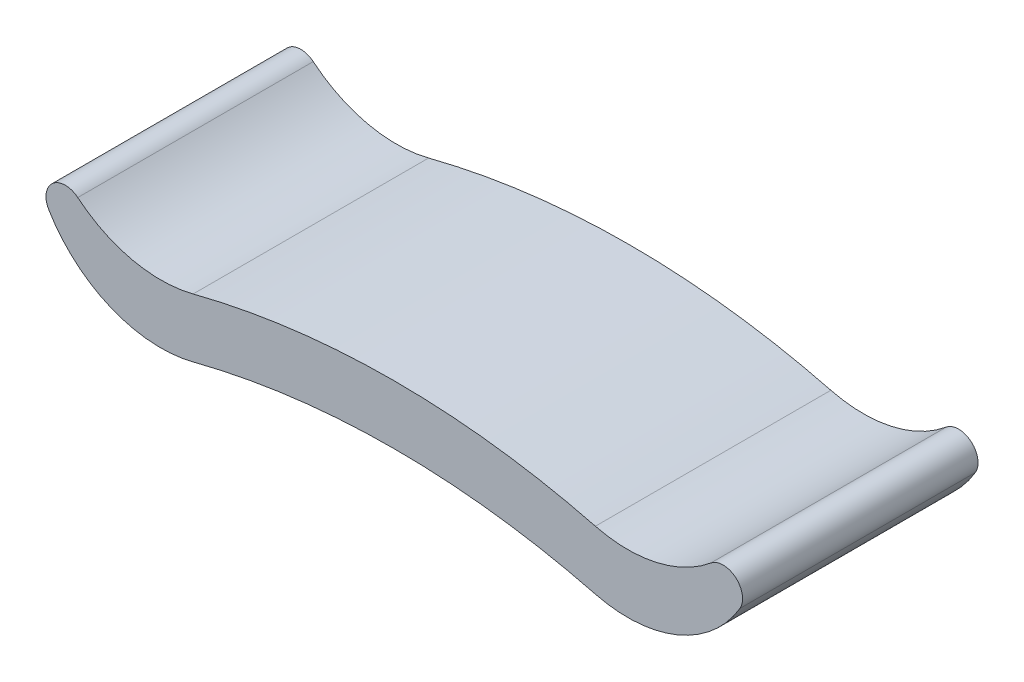
SolidWorks part; units mm, degrees
ref_plane "Ebene vorne" through (0, 0, 0) normal (0, 0, 1) x (1, 0, 0)
ref_plane "Ebene oben" through (0, 0, 0) normal (0, 1, 0) x (1, 0, 0)
ref_plane "Ebene rechts" through (0, 0, 0) normal (1, 0, 0) x (0, 0, -1)
sketch "Skizze1" plane through (0, 0, 0) normal (0, 0, 1) x (1, 0, 0)
  line L0 (0, 110) -> (0, -110) construction
  line L1 (-355, 110) -> (355, 110) construction
  line L2 (-355, 110) -> (-355, -110) construction
  line L3 (-355, -110) -> (355, -110) construction
  line L4 (355, 110) -> (355, -110) construction
  line L5 (0, 105) -> (0, 45)
  line L6 (0, 45) -> (0, -15)
  line L7 (0, -15) -> (0, -75)
  line L8 (-205, 79.1558) -> (-205, -100.8442) construction
  line L9 (-355, 50) -> (0, 50) construction
  line L10 (0, -10) -> (-355, -10) construction
  arc A0 (0, 105) -> (-205, 79.1558) centre (0, -720.9662) ccw
  arc A1 (0, 45) -> (-205, 19.1558) centre (0, -780.9662) ccw
  arc A2 (0, -15) -> (-205, -40.8442) centre (0, -840.9662) ccw
  arc A3 (0, -75) -> (-205, -100.8442) centre (0, -900.9662) ccw
  arc A4 (-205, 79.1558) -> (-322.6026, 105.4617) centre (-237.9641, 207.8158) cw
  arc A5 (-205, 19.1558) -> (-352.2374, 80.128) centre (-237.9641, 147.8158) cw
  arc A6 (-205, -40.8442) -> (-352.2374, 20.128) centre (-237.9641, 87.8158) cw
  arc A7 (-205, -100.8442) -> (-352.2374, -39.872) centre (-237.9641, 27.8158) cw
  arc A8 (-322.6026, 105.4617) -> (-352.2374, 80.128) centre (-335.2124, 90.2124) ccw
  arc A9 (-322.6026, 45.4617) -> (-352.2374, 20.128) centre (-335.2124, 30.2124) ccw
  arc A10 (-322.6026, -14.5383) -> (-352.2374, -39.872) centre (-335.2124, -29.7876) ccw
  point P37 (-237.9641, -105)
  point P38 (-237.9641, -45)
  point P39 (-237.9641, 15)
  point P40 (-237.9641, 75)
  dimension "D1" = 710
  dimension "D2" = 220
  dimension "D3" = 60
  dimension "D4" = 5
  dimension "D5" = 95
  dimension "D6" = 150
extrude "Aufsatz-Linear austragen1" add sketch "Skizze1" along normal mid plane 240 contours A5 A9 A6 A2 L6 A1
mirror "Spiegeln1" about plane through (0, 0, 120) normal (1, 0, 0) of "Aufsatz-Linear austragen1"
